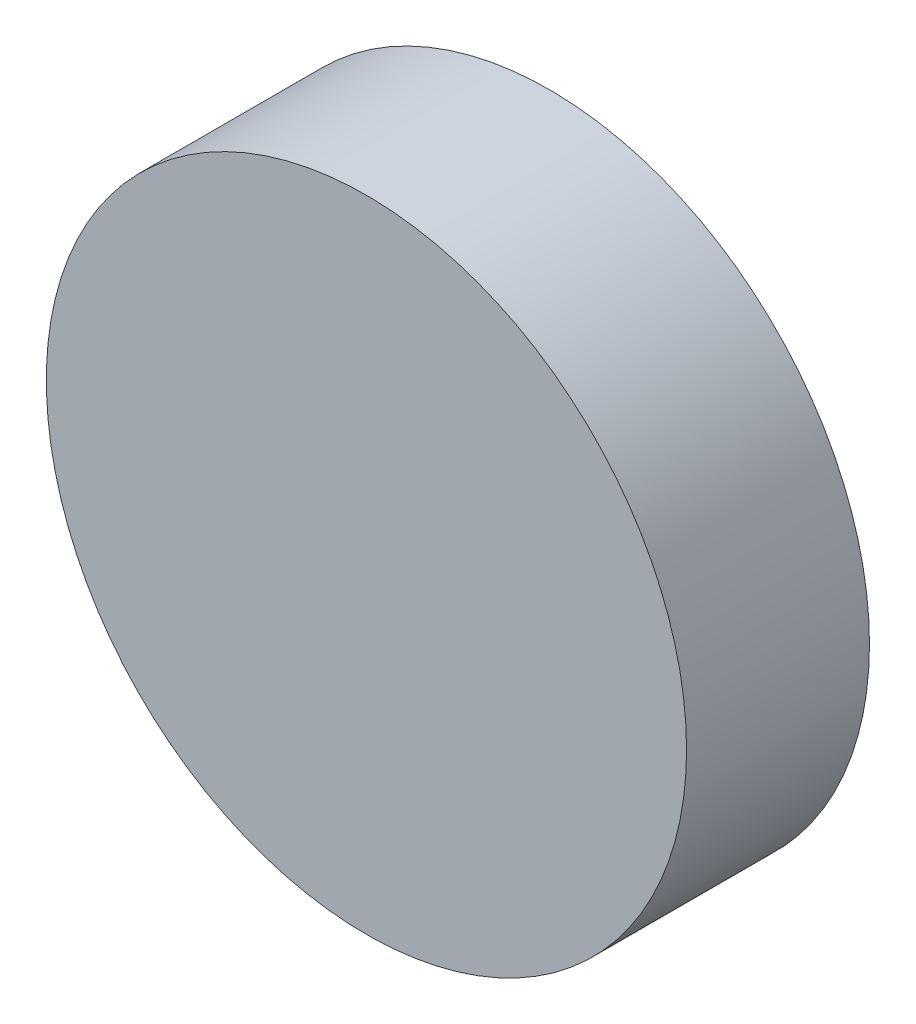
SolidWorks part; units mm, degrees
ref_plane "Front Plane" through (0, 0, 0) normal (0, 0, 1) x (1, 0, 0)
ref_plane "Top Plane" through (0, 0, 0) normal (0, 1, 0) x (1, 0, 0)
ref_plane "Right Plane" through (0, 0, 0) normal (1, 0, 0) x (0, 0, -1)
sketch "Sketch1" plane through (0, 0, 0) normal (0, 0, 1) x (1, 0, 0)
  circle A0 centre (0, 0) radius 5.5562
  dimension "D1" = 11.1125
extrude "Boss-Extrude1" add sketch "Sketch1" along normal blind 3.175
